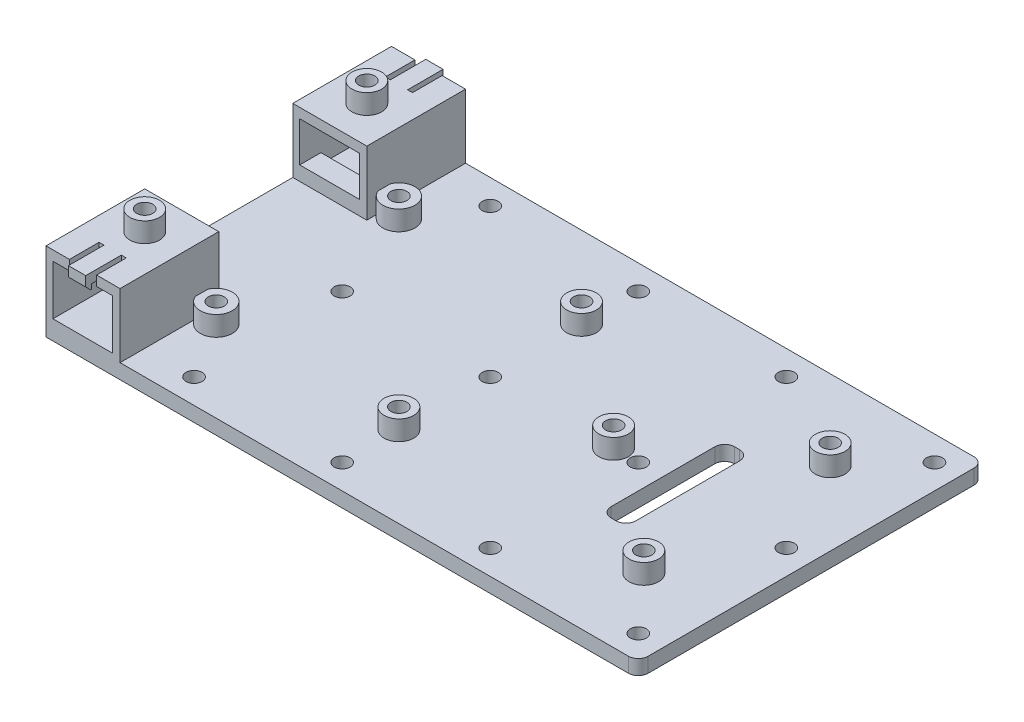
SolidWorks part; units mm, degrees
ref_plane "Front Plane" through (0, 0, 0) normal (0, 0, 1) x (1, 0, 0)
ref_plane "Top Plane" through (0, 0, 0) normal (0, 1, 0) x (1, 0, 0)
ref_plane "Right Plane" through (0, 0, 0) normal (1, 0, 0) x (0, 0, -1)
sketch "Sketch1" plane through (0, 0, 0) normal (0, 1, 0) x (1, 0, 0)
  line L0 (0, 0) -> (103.7225, 0) construction
  line L1 (-60, 35) -> (60, 35)
  line L2 (-60, 35) -> (-60, -35)
  line L3 (-60, -35) -> (60, -35)
  line L4 (60, 35) -> (60, -35)
  line L5 (0, 0) -> (0, 63.2788) construction
  dimension "D1" = 120
  dimension "D2" = 70
extrude "Boss-Extrude1" add sketch "Sketch1" along normal blind 3
sketch "Sketch3" plane through (0, 0, 0) normal (0, -1, 0) x (1, 0, 0)
  line L0 (0, 0) -> (124.6407, 0) construction
  line L1 (60, 35) -> (60, -35) construction
  circle A0 centre (45, 18.875) radius 1.625
  circle A1 centre (45, -18.875) radius 1.625
  point P5 (0, 0)
  dimension "D3" = 3.25
  dimension "D1" = 37.75
  dimension "D2" = 15
sketch "Sketch6" plane through (0, 3, 0) normal (0, 1, 0) x (1, 0, 0)
  line L0 (60, 35) -> (-60, 35) construction
  line L1 (-60, 35) -> (-45, 35)
  line L2 (-60, 35) -> (-60, 15)
  line L3 (-60, 15) -> (-45, 15)
  line L4 (-45, 35) -> (-45, 15)
  line L5 (-60, 0) -> (66.5532, 0) construction
  line L7 (-60, 35) -> (-60, -35) construction
  line L8 (-60, -15) -> (-45, -15)
  line L9 (-45, -35) -> (-45, -15)
  line L10 (-60, -35) -> (-45, -35)
  line L11 (-60, -35) -> (-60, -15)
  dimension "D1" = 15
  dimension "D2" = 20
extrude "Boss-Extrude3" add sketch "Sketch6" along normal blind 13
sketch "Sketch7" plane through (0, 0, -35) normal (0, 0, -1) x (-1, 0, 0)
  line L0 (60, 16) -> (60, 0) construction
  line L1 (46.5, 14) -> (58.6, 14)
  line L2 (46.5, 14) -> (46.5, 3.9)
  line L3 (46.5, 3.9) -> (58.6, 3.9)
  line L4 (58.6, 14) -> (58.6, 3.9)
  line L6 (45, 16) -> (60, 16) construction
  point P8 (58.5, 8.5856)
  dimension "D1" = 12.1
  dimension "D2" = 10.1
  dimension "D3" = 1.4
  dimension "D4" = 2
extrude "Cut-Extrude3" cut sketch "Sketch7" against normal through all
sketch "Sketch8" plane through (0, 3.9, 0) normal (0, 1, 0) x (1, 0, 0)
  line L0 (-45, -35) -> (-45, -15) construction
  line L1 (-60, -15) -> (-45, -15)
  line L2 (-60, -15) -> (-60, -19.3)
  line L3 (-60, -19.3) -> (-45, -19.3)
  line L4 (-45, -15) -> (-45, -19.3)
  dimension "D1" = 4.3
extrude "Boss-Extrude4" add sketch "Sketch8" along normal blind 2
mirror "Mirror1" about plane through (0, 0, 0) normal (0, 0, 1) of "Boss-Extrude4"
sketch "Sketch9" plane through (0, 16, 0) normal (0, 1, 0) x (1, 0, 0)
  line L0 (-45, 35) -> (-60, 35) construction
  line L1 (-55.25, 35) -> (-54.25, 35)
  line L2 (-55.25, 35) -> (-55.25, 29)
  line L3 (-55.25, 29) -> (-54.25, 29)
  line L4 (-54.25, 35) -> (-54.25, 29)
  line L5 (-52.5, 35) -> (-52.5, 20.2316) construction
  line L6 (-50.75, 35) -> (-49.75, 35)
  line L7 (-50.75, 35) -> (-50.75, 29)
  line L8 (-50.75, 29) -> (-49.75, 29)
  line L9 (-49.75, 35) -> (-49.75, 29)
  point P11 (-52.5, 35)
  dimension "D1" = 3.5
  dimension "D2" = 1
  dimension "D3" = 6
extrude "Cut-Extrude4" cut sketch "Sketch9" against normal up to next (2 mm away)
mirror "Mirror2" about plane through (0, 0, 0) normal (0, 0, 1) of "Cut-Extrude4"
sketch "Sketch10" plane through (0, 0, -35) normal (0, 0, -1) x (-1, 0, 0)
  line L0 (54.25, 14) -> (54.25, 16) construction
  line L1 (50.75, 16) -> (54.25, 16)
  line L2 (50.75, 16) -> (50.75, 13)
  line L3 (50.75, 13) -> (54.25, 13)
  line L4 (54.25, 16) -> (54.25, 13)
  line L5 (54.25, 14) -> (50.75, 14) construction
  point P5 (0, 0)
  dimension "D1" = 1
extrude "Boss-Extrude5" add sketch "Sketch10" along normal blind 1.2
chamfer "Chamfer1" distance 1 angle 45 1 edges at (-52.5, 13, -36.2)
mirror "Mirror3" about plane through (0, 0, 0) normal (0, 0, 1) of "Boss-Extrude5", "Chamfer1"
sketch "Sketch11" plane through (0, 0, 0) normal (0, -1, 0) x (1, 0, 0)
  circle A0 centre (20, 0) radius 1.625
  point P2 (0, 0)
  point P4 (0, 0)
  dimension "D1" = 3.25
  dimension "D2" = 20
extrude "Cut-Extrude5" cut sketch "Sketch3" against normal up to next
sketch "Sketch12" plane through (0, 3, 0) normal (0, 1, 0) x (1, 0, 0)
  circle A0 centre (45, 18.875) radius 3
  circle A2 centre (45, 18.875) radius 1.625
  dimension "D1" = 6
  dimension "D2" = 3.25
extrude "Boss-Extrude7" add sketch "Sketch12" along normal blind 4
mirror "Mirror4" about plane through (0, 0, 0) normal (0, 0, 1) of "Boss-Extrude7"
extrude "Cut-Extrude6" cut sketch "Sketch11" against normal up to next contours A0
sketch "Sketch13" plane through (0, 3, 0) normal (0, 1, 0) x (1, 0, 0)
  circle A0 centre (20, 0) radius 3
  circle A1 centre (20, 0) radius 1.625
  dimension "D1" = 3.25
  dimension "D2" = 6
extrude "Boss-Extrude8" add sketch "Sketch13" along normal blind 4
sketch "Sketch14" plane through (0, 3, 0) normal (0, 1, 0) x (1, 0, 0)
  line L0 (-35.6384, 0) -> (1.3616, 0) construction
  line L1 (-42, 18.5) -> (-5, 18.5) construction
  line L2 (-42, 18.5) -> (-42, -18.5) construction
  line L3 (-42, -18.5) -> (-5, -18.5) construction
  line L4 (-5, 18.5) -> (-5, -18.5) construction
  circle A0 centre (-42, 18.5) radius 1.625
  circle A1 centre (-42, -18.5) radius 1.625
  circle A2 centre (-5, 18.5) radius 1.625
  circle A3 centre (-5, -18.5) radius 1.625
  point P10 (-5, 0)
  dimension "D1" = 3.25
  dimension "D2" = 37
  dimension "D3" = 37
  dimension "D4" = 5
extrude "Cut-Extrude7" cut sketch "Sketch14" against normal through all
sketch "Sketch15" plane through (0, 3, 0) normal (0, 1, 0) x (1, 0, 0)
  circle A0 centre (-42, 18.5) radius 3.25
  circle A1 centre (-42, 18.5) radius 1.625
  circle A2 centre (-5, 18.5) radius 3
  circle A3 centre (-5, 18.5) radius 1.625
  circle A4 centre (-5, -18.5) radius 3
  circle A5 centre (-5, -18.5) radius 1.625
  circle A6 centre (-42, -18.5) radius 3.25
  circle A7 centre (-42, -18.5) radius 1.625
  point P7 (0, 0)
  point P8 (-5, 18.5)
  point P13 (-5, -18.5)
  point P18 (-42, -18.5)
  dimension "D1" = 6.5
  dimension "D2" = 3.25
  dimension "D3" = 6
  dimension "D4" = 3.25
  dimension "D5" = 6
  dimension "D6" = 3.25
  dimension "D7" = 6.5
  dimension "D8" = 3.25
extrude "Boss-Extrude13" add sketch "Sketch15" along normal blind 4
sketch "Sketch17" plane through (0, 3, 0) normal (0, 1, 0) x (1, 0, 0)
  line L0 (25.7966, 0) -> (44.0298, 0) construction
  line L1 (30, 12.5) -> (35, 12.5)
  line L2 (30, 12.5) -> (30, -12.5)
  line L3 (30, -12.5) -> (35, -12.5)
  line L4 (35, 12.5) -> (35, -12.5)
  line L5 (60, -35) -> (60, 35) construction
  dimension "D1" = 25
  dimension "D2" = 5
  dimension "D3" = 25
extrude "Cut-Extrude8" cut sketch "Sketch17" against normal through all
sketch "Sketch18" plane through (0, 16, 0) normal (0, 1, 0) x (1, 0, 0)
  line L0 (-60, 15) -> (-45, 15) construction
  line L1 (-60, 35) -> (-60, 15) construction
  circle A0 centre (-52.5, 22.5) radius 3
  circle A1 centre (-52.5, 22.5) radius 1.625
  dimension "D3" = 6
  dimension "D4" = 3.25
  dimension "D1" = 7.5
  dimension "D2" = 7.5
extrude "Boss-Extrude14" add sketch "Sketch18" along normal blind 4
mirror "Mirror5" about plane through (0, 0, 0) normal (0, 0, 1) of "Boss-Extrude14"
fillet "Fillet2" radius 2 6 edges at (30, 1.5, 12.5) (35, 1.5, 12.5) (35, 1.5, -12.5) (30, 1.5, -12.5) (60, 1.5, -35) (60, 1.5, 35)
sketch "Sketch19" plane through (0, 3, 0) normal (0, 1, 0) x (1, 0, 0)
  line L0 (60, -33) -> (60, 33) construction
  line L1 (0, 0) -> (71.8926, 0) construction
  circle A0 centre (55, 0) radius 1.625
  point P8 (0, 0)
  dimension "D1" = 3.25
  dimension "D2" = 5
extrude "Cut-Extrude9" cut sketch "Sketch19" against normal through all
pattern_linear "LPattern1" count 2 spacing 30 along (0, 0, 1) count 2 spacing 30 along (0, 0, -1) of "Cut-Extrude9"
pattern_linear "LPattern2" count 4 spacing 30 along (-1, 0, 0) of "Cut-Extrude9", "LPattern1"
